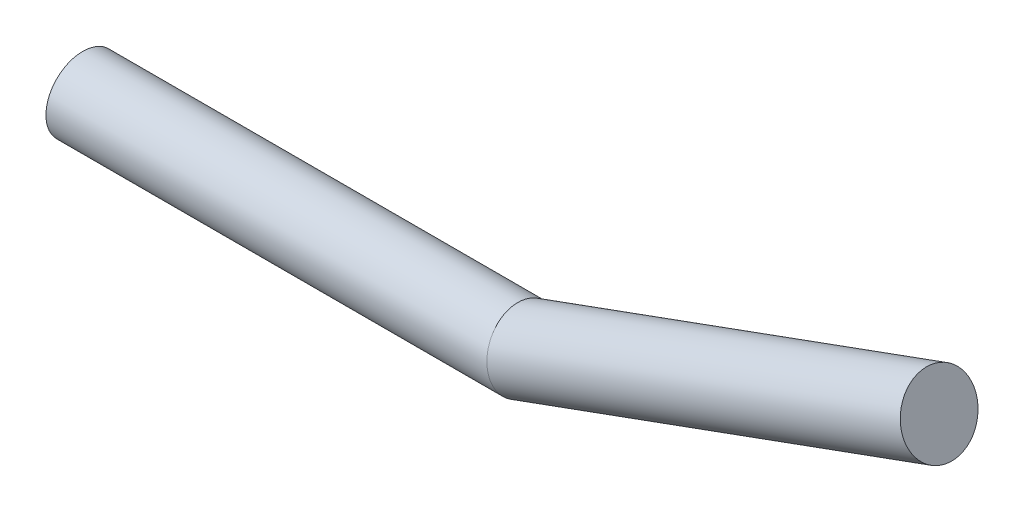
SolidWorks part; units mm, degrees
ref_plane "前视基准面" through (0, 0, 0) normal (0, 0, 1) x (1, 0, 0)
ref_plane "上视基准面" through (0, 0, 0) normal (0, 1, 0) x (1, 0, 0)
ref_plane "右视基准面" through (0, 0, 0) normal (1, 0, 0) x (0, 0, -1)
other "Configuration Table"
sketch "草图1" plane through (0, 0, 0) normal (0, 0, 1) x (1, 0, 0)
  line L0 (0, 0) -> (6, 0)
  line L1 (6, 0) -> (11.6382, 2.0521)
  dimension "D1" = 6
  dimension "D2" = 6
  dimension "D3" = 160
sketch "草图2" plane through (0, 0, 0) normal (1, 0, 0) x (0, 0, -1)
  circle A0 centre (0, 0) radius 0.5
  dimension "D1" = 1
sweep "扫描1" add profiles "草图2" path "草图1"
